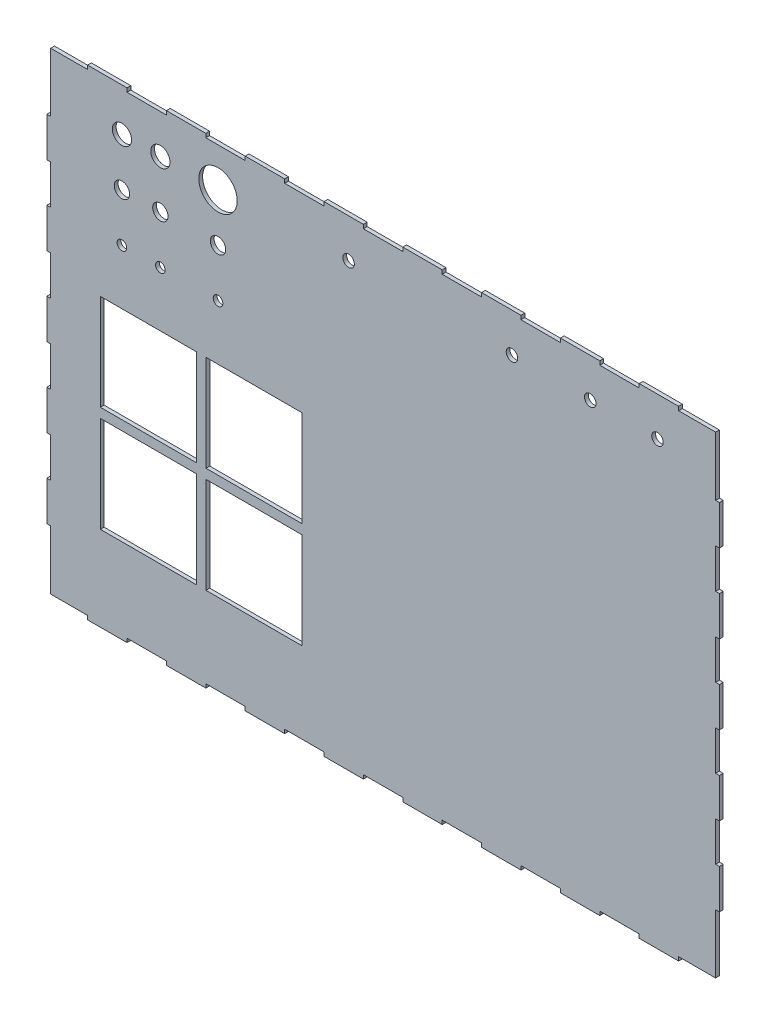
SolidWorks part; units mm, degrees
ref_plane "Front Plane" through (0, 0, 0) normal (0, 0, 1) x (1, 0, 0)
ref_plane "Top Plane" through (0, 0, 0) normal (0, 1, 0) x (1, 0, 0)
ref_plane "Right Plane" through (0, 0, 0) normal (1, 0, 0) x (0, 0, -1)
sketch "Sketch1" plane through (0, 0, 0) normal (0, 0, 1) x (1, 0, 0)
  line B0 (3374.3392, 2517.6226) -> (2104.3392, 2517.6226)
  line B1 (3374.3392, 3787.6226) -> (3374.3392, 2517.6226)
  line B2 (2104.3392, 1120.6226) -> (2104.3392, 2390.6226)
  line B3 (707.3392, 1120.6226) -> (707.3392, 2390.6226)
  line B4 (50.8, 3435.35) -> (50.8, 3956.05)
  circle B5 centre (2263.0932, 4514.0955) radius 63.5
  circle B6 centre (7182.429, 5834.8955) radius 76.2
  line B7 (50.8, 50.8) -> (50.8, 311.15)
  line B8 (50.8, 311.15) -> (50.8, 831.85)
  line B9 (50.8, 831.85) -> (0, 831.85)
  line B10 (0, 831.85) -> (0, 1352.55)
  line B11 (0, 1352.55) -> (50.8, 1352.55)
  line B12 (50.8, 1352.55) -> (50.8, 1873.25)
  line B13 (50.8, 1873.25) -> (0, 1873.25)
  line B14 (0, 1873.25) -> (0, 2393.95)
  line B15 (0, 2393.95) -> (50.8, 2393.95)
  line B16 (50.8, 2393.95) -> (50.8, 2914.65)
  line B17 (50.8, 2914.65) -> (0, 2914.65)
  line B18 (0, 2914.65) -> (0, 3435.35)
  line B19 (0, 3435.35) -> (50.8, 3435.35)
  line B20 (50.8, 3956.05) -> (0, 3956.05)
  line B21 (0, 3956.05) -> (0, 4476.75)
  line B22 (0, 4476.75) -> (50.8, 4476.75)
  line B23 (50.8, 4476.75) -> (50.8, 4997.45)
  line B24 (50.8, 4997.45) -> (0, 4997.45)
  line B25 (0, 4997.45) -> (0, 5518.15)
  line B26 (0, 5518.15) -> (50.8, 5518.15)
  line B27 (50.8, 5518.15) -> (50.8, 6299.2)
  line B28 (50.8, 6299.2) -> (539.75, 6299.2)
  line B29 (539.75, 6299.2) -> (539.75, 6350)
  line B30 (539.75, 6350) -> (1060.45, 6350)
  line B31 (1060.45, 6350) -> (1060.45, 6299.2)
  line B32 (1060.45, 6299.2) -> (1581.15, 6299.2)
  line B33 (1581.15, 6299.2) -> (1581.15, 6350)
  line B34 (1581.15, 6350) -> (2101.85, 6350)
  line B35 (2101.85, 6350) -> (2101.85, 6299.2)
  line B36 (2101.85, 6299.2) -> (2622.55, 6299.2)
  line B37 (2622.55, 6299.2) -> (2622.55, 6350)
  line B38 (2622.55, 6350) -> (3143.25, 6350)
  line B39 (3143.25, 6350) -> (3143.25, 6299.2)
  line B40 (3143.25, 6299.2) -> (3663.95, 6299.2)
  line B41 (3663.95, 6299.2) -> (3663.95, 6350)
  line B42 (3663.95, 6350) -> (4184.65, 6350)
  line B43 (4184.65, 6350) -> (4184.65, 6299.2)
  line B44 (4184.65, 6299.2) -> (4705.35, 6299.2)
  line B45 (4705.35, 6299.2) -> (4705.35, 6350)
  line B46 (4705.35, 6350) -> (5226.05, 6350)
  line B47 (5226.05, 6350) -> (5226.05, 6299.2)
  line B48 (5226.05, 6299.2) -> (5746.75, 6299.2)
  line B49 (5746.75, 6299.2) -> (5746.75, 6350)
  line B50 (5746.75, 6350) -> (6267.45, 6350)
  line B51 (6267.45, 6350) -> (6267.45, 6299.2)
  line B52 (6267.45, 6299.2) -> (6788.15, 6299.2)
  line B53 (6788.15, 6299.2) -> (6788.15, 6350)
  line B54 (6788.15, 6350) -> (7308.85, 6350)
  line B55 (7308.85, 6350) -> (7308.85, 6299.2)
  line B56 (7308.85, 6299.2) -> (7829.55, 6299.2)
  line B57 (7829.55, 6299.2) -> (7829.55, 6350)
  line B58 (7829.55, 6350) -> (8350.25, 6350)
  line B59 (8350.25, 6350) -> (8350.25, 6299.2)
  line B60 (8350.25, 6299.2) -> (8839.2, 6299.2)
  line B61 (8839.2, 6299.2) -> (8839.2, 6038.85)
  line B62 (8839.2, 6038.85) -> (8839.2, 5518.15)
  line B63 (8839.2, 5518.15) -> (8890, 5518.15)
  line B64 (8890, 5518.15) -> (8890, 4997.45)
  line B65 (8890, 4997.45) -> (8839.2, 4997.45)
  line B66 (8839.2, 4997.45) -> (8839.2, 4476.75)
  line B67 (8839.2, 4476.75) -> (8890, 4476.75)
  line B68 (8890, 4476.75) -> (8890, 3956.05)
  line B69 (8890, 3956.05) -> (8839.2, 3956.05)
  line B70 (8839.2, 3956.05) -> (8839.2, 3435.35)
  line B71 (8839.2, 3435.35) -> (8890, 3435.35)
  line B72 (8890, 3435.35) -> (8890, 2914.65)
  line B73 (8890, 2914.65) -> (8839.2, 2914.65)
  line B74 (8839.2, 2914.65) -> (8839.2, 2393.95)
  line B75 (8839.2, 2393.95) -> (8890, 2393.95)
  line B76 (8890, 2393.95) -> (8890, 1873.25)
  line B77 (8890, 1873.25) -> (8839.2, 1873.25)
  line B78 (8839.2, 1873.25) -> (8839.2, 1352.55)
  line B79 (8839.2, 1352.55) -> (8890, 1352.55)
  line B80 (8890, 1352.55) -> (8890, 831.85)
  line B81 (8890, 831.85) -> (8839.2, 831.85)
  line B82 (8839.2, 831.85) -> (8839.2, 50.8)
  line B83 (8839.2, 50.8) -> (8350.25, 50.8)
  line B84 (8350.25, 50.8) -> (8350.25, 0)
  line B85 (8350.25, 0) -> (7829.55, 0)
  line B86 (7829.55, 0) -> (7829.55, 50.8)
  line B87 (7829.55, 50.8) -> (7308.85, 50.8)
  line B88 (7308.85, 50.8) -> (7308.85, 0)
  line B89 (7308.85, 0) -> (6788.15, 0)
  line B90 (6788.15, 0) -> (6788.15, 50.8)
  line B91 (6788.15, 50.8) -> (6267.45, 50.8)
  line B92 (6267.45, 50.8) -> (6267.45, 0)
  line B93 (6267.45, 0) -> (5746.75, 0)
  line B94 (5746.75, 0) -> (5746.75, 50.8)
  line B95 (5746.75, 50.8) -> (5226.05, 50.8)
  line B96 (5226.05, 50.8) -> (5226.05, 0)
  line B97 (5226.05, 0) -> (4705.35, 0)
  line B98 (4705.35, 0) -> (4705.35, 50.8)
  line B99 (4705.35, 50.8) -> (4184.65, 50.8)
  line B100 (4184.65, 50.8) -> (4184.65, 0)
  line B101 (4184.65, 0) -> (3663.95, 0)
  line B102 (3663.95, 0) -> (3663.95, 50.8)
  line B103 (3663.95, 50.8) -> (3143.25, 50.8)
  line B104 (3143.25, 50.8) -> (3143.25, 0)
  line B105 (3143.25, 0) -> (2622.55, 0)
  line B106 (2622.55, 0) -> (2622.55, 50.8)
  line B107 (2622.55, 50.8) -> (2101.85, 50.8)
  line B108 (2101.85, 50.8) -> (2101.85, 0)
  line B109 (2101.85, 0) -> (1581.15, 0)
  line B110 (1581.15, 0) -> (1581.15, 50.8)
  line B111 (1581.15, 50.8) -> (1060.45, 50.8)
  line B112 (1060.45, 50.8) -> (1060.45, 0)
  line B113 (1060.45, 0) -> (539.75, 0)
  line B114 (539.75, 0) -> (539.75, 50.8)
  line B115 (539.75, 50.8) -> (50.8, 50.8)
  circle B116 centre (6147.9003, 5834.8955) radius 76.2
  circle B117 centre (8071.429, 5834.8955) radius 76.2
  circle B118 centre (3988.9003, 5834.8955) radius 76.2
  circle B119 centre (993.0932, 5784.0955) radius 127
  circle B120 centre (993.0932, 5149.0955) radius 101.6
  circle B121 centre (993.0932, 4514.0955) radius 63.5
  circle B122 centre (1501.0932, 5784.0955) radius 127
  circle B123 centre (1501.0932, 5149.0955) radius 101.6
  circle B124 centre (1501.0932, 4514.0955) radius 63.5
  circle B125 centre (2263.0932, 5784.0955) radius 254
  circle B126 centre (2263.0932, 5149.0955) radius 101.6
  line B127 (2104.3392, 2517.6226) -> (2104.3392, 3787.6226)
  line B128 (2104.3392, 3787.6226) -> (3374.3392, 3787.6226)
  line B129 (2104.3392, 2390.6226) -> (3374.3392, 2390.6226)
  line B130 (3374.3392, 2390.6226) -> (3374.3392, 1120.6226)
  line B131 (3374.3392, 1120.6226) -> (2104.3392, 1120.6226)
  line B132 (707.3392, 2390.6226) -> (1977.3392, 2390.6226)
  line B133 (1977.3392, 2390.6226) -> (1977.3392, 1120.6226)
  line B134 (1977.3392, 1120.6226) -> (707.3392, 1120.6226)
  line B135 (707.3392, 2517.6226) -> (707.3392, 3787.6226)
  line B136 (707.3392, 3787.6226) -> (1977.3392, 3787.6226)
  line B137 (1977.3392, 3787.6226) -> (1977.3392, 2517.6226)
  line B138 (1977.3392, 2517.6226) -> (707.3392, 2517.6226)
sketch_block_instance "top-1"
sketch_block "top"
extrude "Boss-Extrude1" add sketch "Sketch1" along normal blind 50
scale "Scale1" scale about centroid uniform scaling yes scale factor 0.04
